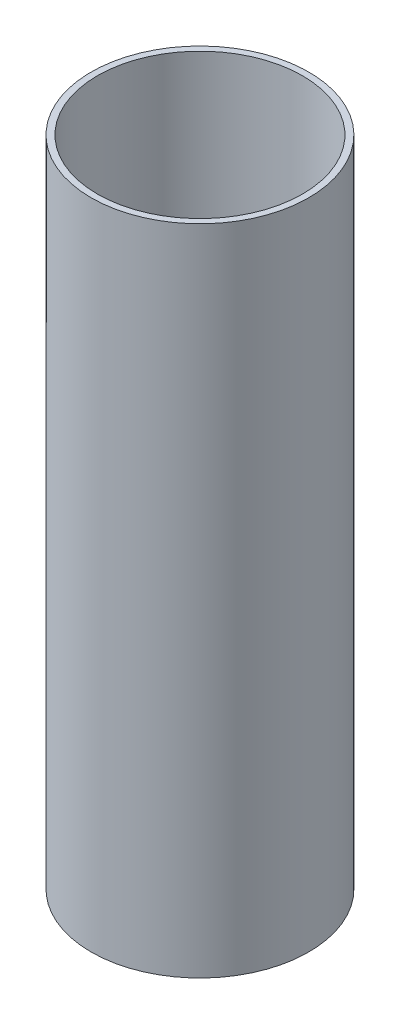
SolidWorks part; units mm, degrees
ref_plane "Front Plane" through (0, 0, 0) normal (0, 0, 1) x (1, 0, 0)
ref_plane "Top Plane" through (0, 0, 0) normal (0, 1, 0) x (1, 0, 0)
ref_plane "Right Plane" through (0, 0, 0) normal (1, 0, 0) x (0, 0, -1)
sketch "Sketch1" plane through (0, 0, 0) normal (0, 1, 0) x (1, 0, 0)
  circle A0 centre (0, 0) radius 6.35
  circle A1 centre (0, 0) radius 5.9808
  dimension "D1" = 12.7
  dimension "D2" = 11.9615
sketch "Sketch2" plane through (0, 0, 0) normal (1, 0, 0) x (0, 0, -1)
  line L0 (0, 0) -> (0, -38.1)
  dimension "D1" = 38.1
sweep "Sweep1" add profiles "Sketch1" path "Sketch2"
